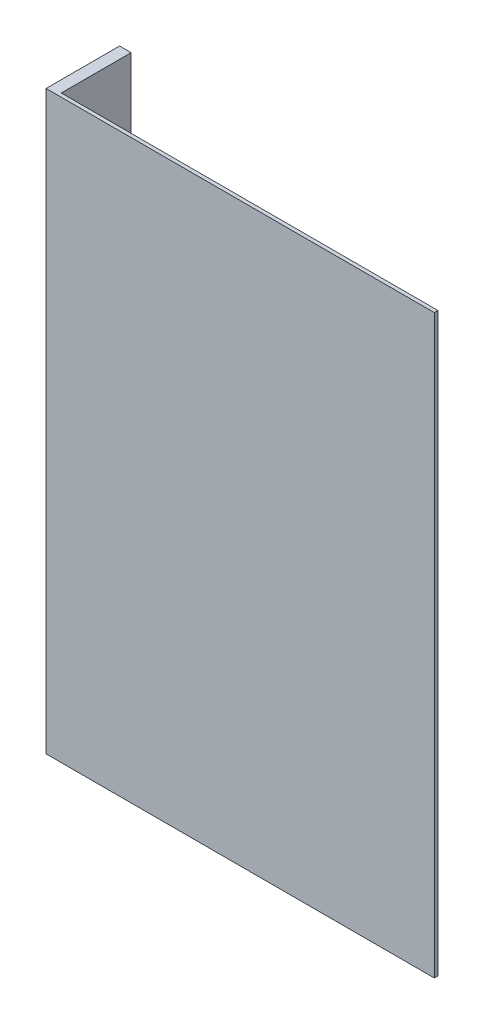
SolidWorks part; units mm, degrees
ref_plane "Front Plane" through (0, 0, 0) normal (0, 0, 1) x (1, 0, 0)
ref_plane "Top Plane" through (0, 0, 0) normal (0, 1, 0) x (1, 0, 0)
ref_plane "Right Plane" through (0, 0, 0) normal (1, 0, 0) x (0, 0, -1)
sketch "Sketch1" plane through (0, 0, 0) normal (0, 0, 1) x (1, 0, 0)
  line L0 (2.5917, 2.54) -> (2.5917, -124.46)
  line L7 (-72.4142, -124.46) -> (2.5917, -124.46)
  line L8 (2.5917, 2.54) -> (-72.4142, 2.54)
  line L9 (2.5917, 2.54) -> (-80.4142, 2.54) construction
  line L10 (-72.4142, 2.54) -> (-72.4142, -121.92)
  line L11 (2.5917, -121.92) -> (-80.4142, -121.92) construction
  line L12 (-72.4142, -121.92) -> (-72.4142, -124.46)
  dimension "D1" = 8
extrude "Boss-Extrude1" add sketch "Sketch1" along normal blind 0.8
sketch "Sketch2" plane through (0, 0, 0) normal (0, 0, 1) x (1, 0, 0)
  line L4 (-72.4142, 2.54) -> (-72.4142, -124.46) construction
  line L6 (-72.4142, -124.46) -> (-80.4142, -124.46)
  line L10 (-72.4142, -112.46) -> (-72.4142, -124.46)
  line L12 (-72.4142, 2.54) -> (-72.4142, -9.46)
  line L17 (-80.4142, -124.46) -> (-82.9542, -124.46)
  line L18 (-82.9542, -124.46) -> (-82.9542, -112.46)
  line L19 (-82.9542, -124.46) -> (-82.9542, -85.96) construction
  line L21 (-82.9542, 2.54) -> (-82.9542, -112.46)
  line L22 (-72.4142, 2.54) -> (-82.9542, 2.54)
  line L23 (-72.4142, -9.46) -> (-72.4142, -112.46)
extrude "Boss-Extrude2" add sketch "Sketch2" along normal blind 0.8
sketch "Sketch3" plane through (0, 0, 0) normal (0, 0, -1) x (-1, 0, 0)
  line L0 (82.9542, 2.54) -> (80.4142, 2.54)
  line L1 (80.4142, 2.54) -> (80.4142, 0) construction
  line L2 (-2.5917, 2.54) -> (82.9542, 2.54) construction
  line L3 (80.4142, 2.54) -> (80.4142, -9.46)
  line L6 (82.9542, -9.46) -> (82.9542, 2.54)
  line L7 (82.9542, -124.46) -> (80.4142, -124.46)
  line L8 (82.9542, -124.46) -> (-2.5917, -124.46) construction
  line L9 (80.4142, -121.92) -> (80.4142, -124.46) construction
  line L10 (80.4142, -124.46) -> (80.4142, -112.46)
  line L13 (82.9542, -112.46) -> (82.9542, -124.46)
  line L14 (80.4142, -9.46) -> (80.4142, -112.46)
  line L15 (82.9542, -9.46) -> (82.9542, -112.46)
extrude "Boss-Extrude3" add sketch "Sketch3" along normal up to surface (15.4 mm away)
